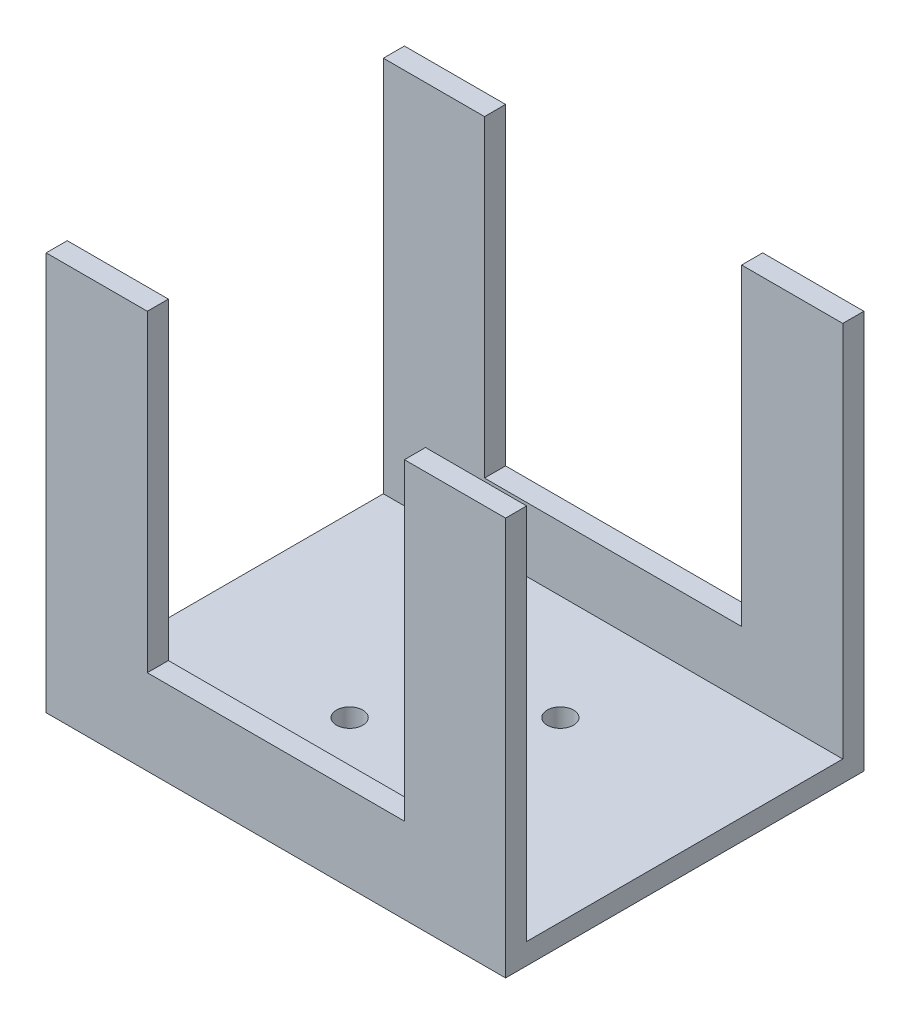
SolidWorks part; units mm, degrees
ref_plane "Front Plane" through (0, 0, 0) normal (0, 0, 1) x (1, 0, 0)
ref_plane "Top Plane" through (0, 0, 0) normal (0, 1, 0) x (1, 0, 0)
ref_plane "Right Plane" through (0, 0, 0) normal (1, 0, 0) x (0, 0, -1)
sketch "Sketch1" plane through (0, 0, 0) normal (0, 1, 0) x (1, 0, 0)
  line L5 (-21.8, -17) -> (21.8, -17)
  line L6 (-21.8, -17) -> (-21.8, 17)
  line L7 (-21.8, 17) -> (21.8, 17)
  line L8 (21.8, -17) -> (21.8, 17)
  line L9 (-21.8, -17) -> (21.8, 17) construction
  line L10 (-21.8, 17) -> (21.8, -17) construction
  point P0 (0, 0)
extrude "Boss-Extrude1" add sketch "Sketch1" along normal blind 2
sketch "Sketch2" plane through (0, 2, 0) normal (0, 1, 0) x (1, 0, 0)
  line L0 (21.8, -17) -> (21.8, 17) construction
  line L1 (-21.8, 17) -> (21.8, 17)
  line L2 (-21.8, 17) -> (-21.8, 15)
  line L3 (-21.8, 15) -> (21.8, 15)
  line L4 (21.8, 17) -> (21.8, 15)
  line L5 (-1.1, 0) -> (1.1, 0) construction
  line L6 (-21.8, -15) -> (21.8, -15)
  line L7 (21.8, -17) -> (21.8, -15)
  line L8 (-21.8, -17) -> (21.8, -17)
  line L9 (-21.8, -17) -> (-21.8, -15)
extrude "Boss-Extrude2" add sketch "Sketch2" along normal blind 35.8
sketch "Sketch3" plane through (0, 0, 17) normal (0, 0, 1) x (1, 0, 0)
  line L9 (-21.8, 37.8) -> (21.8, 37.8) construction
  line L10 (12.2, 37.8) -> (-12.2, 37.8)
  line L11 (0, 37.8) -> (0, 8.09)
  line L12 (12.2, 8.09) -> (-12.2, 8.09)
  line L13 (-12.2, 37.8) -> (-12.2, 8.09)
  line L14 (0, -18.7) -> (0, 18.7) construction
  line L15 (12.2, 37.8) -> (12.2, 8.09)
  point P1 (3.8134, 37.8)
  line M15 (21.8, 37.8) -> (-21.8, 37.8)
extrude "Cut-Extrude2" cut sketch "Sketch3" against normal blind 66.8 contours L10 L13 L12 L11 | L15 L11 L12 M15
sketch "Sketch4" plane through (0, 2, 0) normal (0, 1, 0) x (1, 0, 0)
  line L1 (-5, -5) -> (5, -5)
  line L2 (-5, -5) -> (-5, 5)
  line L3 (-5, 5) -> (5, 5)
  line L4 (5, -5) -> (5, 5)
  line L5 (-5, -5) -> (5, 5) construction
  line L6 (-5, 5) -> (5, -5) construction
  circle A0 centre (-5, 5) radius 1.25
  circle A1 centre (5, 5) radius 1.25
  circle A2 centre (5, -5) radius 1.25
  circle A3 centre (-5, -5) radius 1.25
  point P0 (0, 0)
  point P16 (0, 0)
  dimension "D1" = 4
extrude "Cut-Extrude3" cut sketch "Sketch4" against normal blind 66.8 contours L2 A0 L3 | L4 A1 L3 | L3 A1 L4 | L3 A0 L2 | L2 A3 L1 | L1 A2 L4 | L1 A3 L2 | L4 A2 L1
sketch "Sketch5" plane through (0, 0, 0) normal (0, -1, 0) x (-1, 0, 0)
  circle A0 centre (0, 0) radius 11.7492
